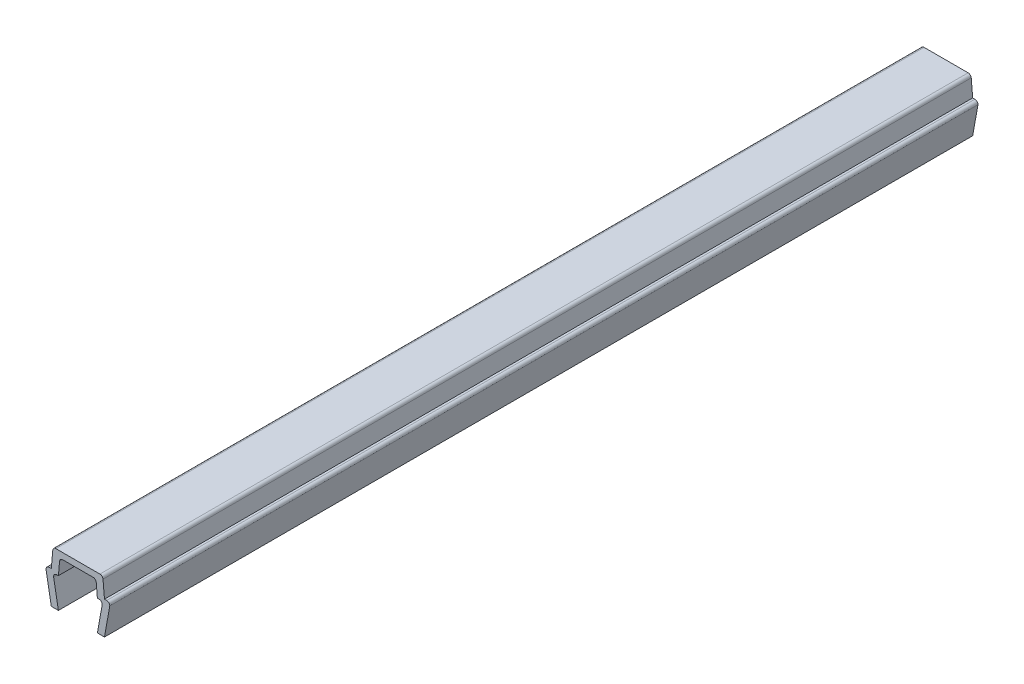
SolidWorks part; units mm, degrees
ref_plane "Front Plane" through (0, 0, 0) normal (0, 0, 1) x (1, 0, 0)
ref_plane "Top Plane" through (0, 0, 0) normal (0, 1, 0) x (1, 0, 0)
ref_plane "Right Plane" through (0, 0, 0) normal (1, 0, 0) x (0, 0, -1)
ref_plane "Plane1" through (0, 0, 0) normal (0, 0, 1) x (1, 0, 0)
sketch "Sketch1" plane through (0, 0, 0) normal (0, 0, 1) x (1, 0, 0)
  line L0 (-3.6, 3.35) -> (-3, 0)
  line L1 (-3, 0) -> (-2.2, 0)
  line L2 (-2.2, 0) -> (-2.7352, 2.9883)
  line L3 (-2.3907, 3.4) -> (-2.2, 3.4)
  line L4 (-2.2, 3.4) -> (-2.0705, 4.8805)
  line L5 (-1.7218, 5.2) -> (1.7218, 5.2)
  line L6 (2.0705, 4.8805) -> (2.2, 3.4)
  line L7 (2.2, 3.4) -> (2.3907, 3.4)
  line L8 (2.7352, 2.9883) -> (2.2, 0)
  line L9 (2.2, 0) -> (3, 0)
  line L10 (3, 0) -> (3.6, 3.35)
  line L11 (3.25, 3.7) -> (3, 3.7)
  line L12 (3, 3.7) -> (2.8355, 5.5805)
  line L13 (2.4868, 5.9) -> (-2.4868, 5.9)
  line L14 (-2.8355, 5.5805) -> (-3, 3.7)
  line L15 (-3, 3.7) -> (-3.25, 3.7)
  arc A0 (-2.7352, 2.9883) -> (-2.3907, 3.4) centre (-2.3907, 3.05) cw
  arc A1 (-2.0705, 4.8805) -> (-1.7218, 5.2) centre (-1.7218, 4.85) cw
  arc A2 (1.7218, 5.2) -> (2.0705, 4.8805) centre (1.7218, 4.85) cw
  arc A3 (2.3907, 3.4) -> (2.7352, 2.9883) centre (2.3907, 3.05) cw
  arc A4 (3.6, 3.35) -> (3.25, 3.7) centre (3.25, 3.35) ccw
  arc A5 (2.8355, 5.5805) -> (2.4868, 5.9) centre (2.4868, 5.55) ccw
  arc A6 (-2.4868, 5.9) -> (-2.8355, 5.5805) centre (-2.4868, 5.55) ccw
  arc A7 (-3.25, 3.7) -> (-3.6, 3.35) centre (-3.25, 3.35) ccw
extrude "Boss-Extrude1" add sketch "Sketch1" against normal mid plane 98
